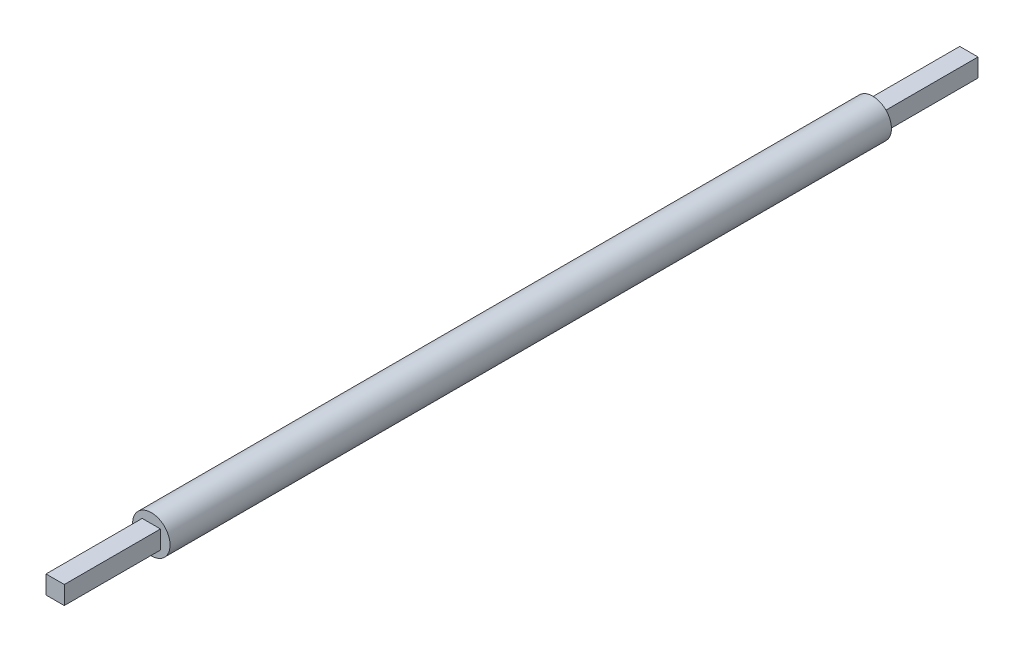
SolidWorks part; units mm, degrees
material "PLA Aero Bambu"
ref_plane "Front Plane" through (0, 0, 0) normal (0, 0, 1) x (1, 0, 0)
ref_plane "Top Plane" through (0, 0, 0) normal (0, 1, 0) x (1, 0, 0)
ref_plane "Right Plane" through (0, 0, 0) normal (1, 0, 0) x (0, 0, -1)
sketch "Sketch1" plane through (0, 0, 0) normal (0, 0, 1) x (1, 0, 0)
  circle A0 centre (0, 0) radius 0.975
  dimension "D1" = 1.95
extrude "Boss-Extrude2" add sketch "Sketch1" along normal blind 18.75
sketch "Sketch2" plane through (0, 0, 18.75) normal (0, 0, 1) x (1, 0, 0)
  line L1 (-0.475, 0.475) -> (0.475, 0.475)
  line L2 (-0.475, 0.475) -> (-0.475, -0.475)
  line L3 (-0.475, -0.475) -> (0.475, -0.475)
  line L4 (0.475, 0.475) -> (0.475, -0.475)
  point P4 (0, -0.475)
  point P6 (-0.475, 0)
  dimension "D1" = 0.95
extrude "Boss-Extrude3" add sketch "Sketch2" along normal blind 5
mirror "Mirror1" about plane through (0, 0, 0) normal (0, 0, 1) of "Boss-Extrude3", "Boss-Extrude2"
